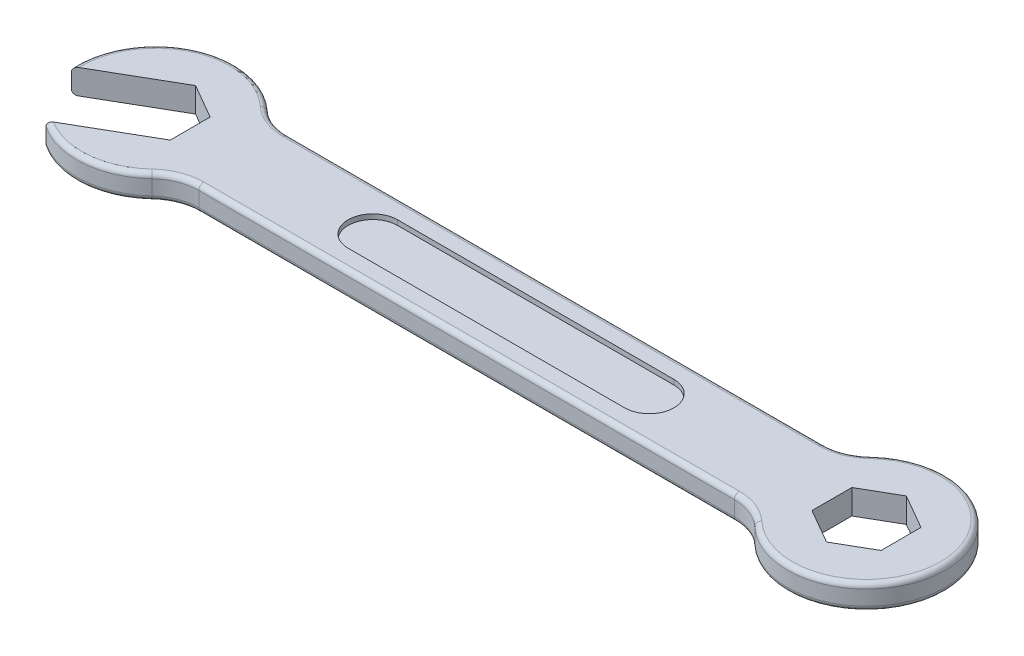
SolidWorks part; units mm, degrees
material "Alloy Steel"
ref_plane "Front Plane" through (0, 0, 0) normal (0, 0, 1) x (1, 0, 0)
ref_plane "Top Plane" through (0, 0, 0) normal (0, 1, 0) x (1, 0, 0)
ref_plane "Right Plane" through (0, 0, 0) normal (1, 0, 0) x (0, 0, -1)
sketch "Sketch1" plane through (0, 0, 0) normal (0, 1, 0) x (1, 0, 0)
  line L0 (0, 0) -> (83.2773, 0) construction
  line L1 (0, 0) -> (-10.3537, -5.9777) construction
  line L2 (6.6144, 4.5) -> (65.3856, 4.5)
  line L4 (-4.48, -6.628) -> (3.5, -2.0207)
  line L5 (3.5, -2.0207) -> (3.5, 2.0207)
  line L6 (3.5, 2.0207) -> (0, 4.0415)
  line L7 (0, 4.0415) -> (-7.98, -0.5658)
  line L9 (-3.5, 2.0207) -> (-3.5, 0) [skipped]
  line L10 (-1.75, -3.0311) -> (0, -4.0415) [skipped]
  line L11 (6.6144, -4.5) -> (65.3856, -4.5)
  line L13 (72, 4.0415) -> (68.5, 2.0207)
  line L14 (68.5, 2.0207) -> (68.5, -2.0207)
  line L15 (68.5, -2.0207) -> (72, -4.0415)
  line L16 (72, -4.0415) -> (75.5, -2.0207)
  line L17 (75.5, -2.0207) -> (75.5, 2.0207)
  line L18 (75.5, 2.0207) -> (72, 4.0415)
  arc A0 (-4.48, -6.628) -> (6.6144, -4.5) centre (0, 0) ccw
  circle A2 centre (0, 0) radius 3.5 construction
  arc A3 (65.3856, -4.5) -> (65.3856, 4.5) centre (72, 0) ccw
  arc A4 (6.6144, 4.5) -> (-7.98, -0.5658) centre (0, 0) ccw
  circle A5 centre (72, 0) radius 3.5 construction
  dimension "D1" = 8
  dimension "D2" = 7
  dimension "D5" = 72
  dimension "D6" = 8
  dimension "D8" = 7
  dimension "D3" = 30
  dimension "D4" = 7
  dimension "D7" = 9
extrude "Boss-Extrude1" add sketch "Sketch1" along normal mid plane 2.5
fillet "Fillet1" radius 5 4 edges at (65.3856, 0, -4.5) (65.3856, 0, 4.5) (6.6144, 0, 4.5) (6.6144, 0, -4.5)
fillet "Fillet2" radius 0.5 18 edges at (-3.4445, -1.25, -7.2205) (7.0396, -1.25, -4.8487) (36, -1.25, -4.5) (64.9604, -1.25, -4.8487) (80, -1.25, 0) (64.9604, -1.25, 4.8487) (36, -1.25, 4.5) (7.0396, -1.25, 4.8487) (-3.4445, 1.25, -7.2205) (7.0396, 1.25, -4.8487) (36, 1.25, -4.5) (64.9604, 1.25, -4.8487) (80, 1.25, 0) (64.9604, 1.25, 4.8487) (36, 1.25, 4.5) (7.0396, 1.25, 4.8487) (0.6272, -1.25, 7.9754) (0.6272, 1.25, 7.9754)
sketch "Sketch2" plane through (0, 1.25, 0) normal (0, 1, 0) x (1, 0, 0)
  line L0 (22, 0) -> (50, 0) construction
  line L1 (22, 2.5) -> (50, 2.5)
  line L2 (22, -2.5) -> (50, -2.5)
  arc A0 (22, 2.5) -> (22, -2.5) centre (22, 0) ccw
  arc A1 (50, -2.5) -> (50, 2.5) centre (50, 0) ccw
  point P2 (36, 0)
  dimension "D2" = 2.5
  dimension "D1" = 22
  dimension "D3" = 28
extrude "Cut-Extrude1" cut sketch "Sketch2" against normal blind 0.5
mirror "Mirror1" about plane through (0, 0, 0) normal (0, 1, 0) of "Cut-Extrude1"
